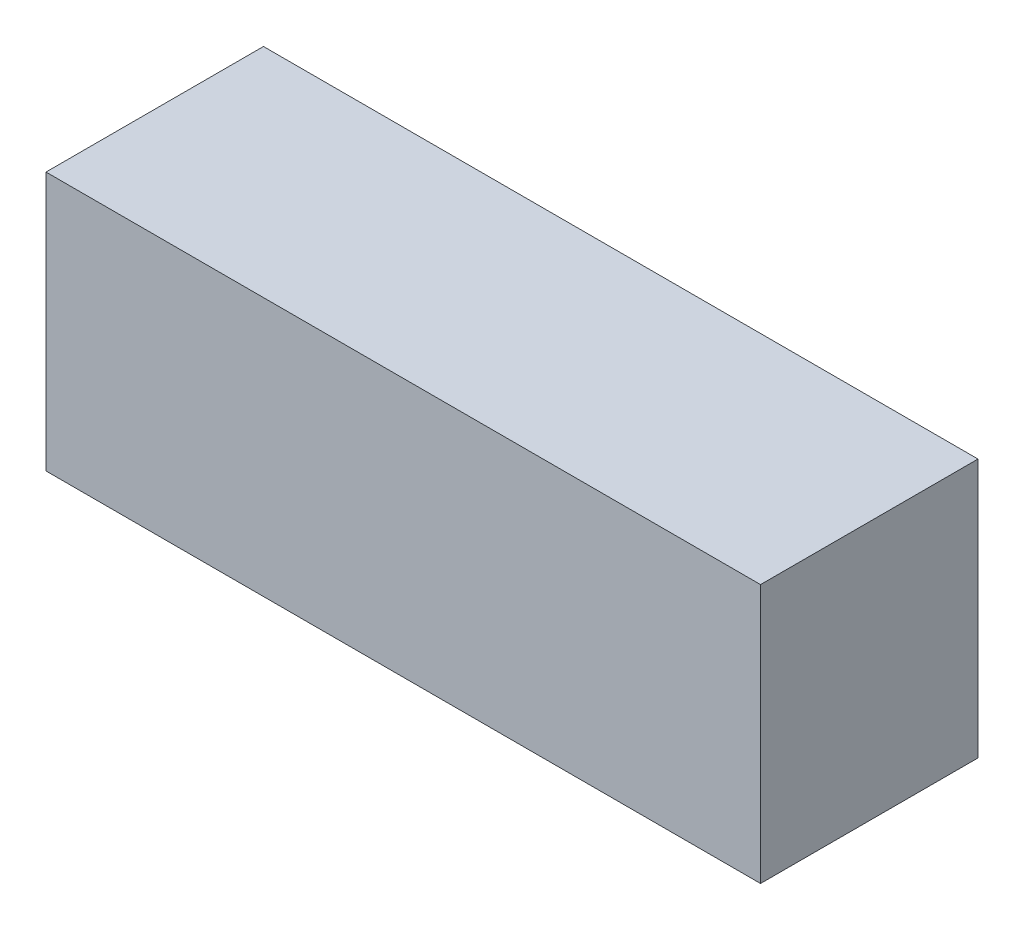
SolidWorks part; units mm, degrees
ref_plane "Front" through (0, 0, 0) normal (0, 0, 1) x (1, 0, 0)
ref_plane "Top" through (0, 0, 0) normal (0, 1, 0) x (1, 0, 0)
ref_plane "Right" through (0, 0, 0) normal (1, 0, 0) x (0, 0, -1)
sketch "Sketch1" plane through (0, 0, 0) normal (0, 0, 1) x (1, 0, 0)
  line L1 (-26.289, -9.525) -> (26.289, -9.525)
  line L2 (-26.289, -9.525) -> (-26.289, 9.525)
  line L3 (-26.289, 9.525) -> (26.289, 9.525)
  line L4 (26.289, -9.525) -> (26.289, 9.525)
  line L5 (-26.289, -9.525) -> (26.289, 9.525) construction
  line L6 (-26.289, 9.525) -> (26.289, -9.525) construction
  point P0 (0, 0)
  dimension "D1" = 19.05
  dimension "D2" = 52.578
extrude "Boss-Extrude1" add sketch "Sketch1" along normal blind 16.002
sketch "Build Plans" plane through (0, 0, 16.002) normal (0, 0, 1) x (1, 0, 0)
  line L0 (26.289, 9.525) -> (26.289, 28.575)
  line L2 (-26.289, 28.575) -> (-26.289, 9.525)
  line L4 (26.289, -9.525) -> (26.289, 9.525)
  line L5 (26.289, 9.525) -> (-26.289, 9.525)
  line L6 (-26.289, 9.525) -> (-26.289, -9.525)
  line L7 (-26.289, -9.525) -> (26.289, -9.525)
  line L8 (26.289, -9.525) -> (26.289, 9.525)
  line L9 (26.289, 9.525) -> (-26.289, 9.525)
  line L10 (-26.289, 9.525) -> (-26.289, -9.525)
  line L11 (-26.289, -9.525) -> (26.289, -9.525)
  line L12 (26.289, 28.575) -> (26.289, 47.625)
  line L13 (26.289, 47.625) -> (-26.289, 47.625)
  line L14 (-26.289, 47.625) -> (-26.289, 28.575)
  line L15 (-26.289, 28.575) -> (26.289, 28.575)
  line L20 (-26.289, 9.525) -> (26.289, 9.525)
  line L21 (26.289, 28.575) -> (-26.289, 28.575)
  dimension "D1" = 0
  dimension "D2" = 3
